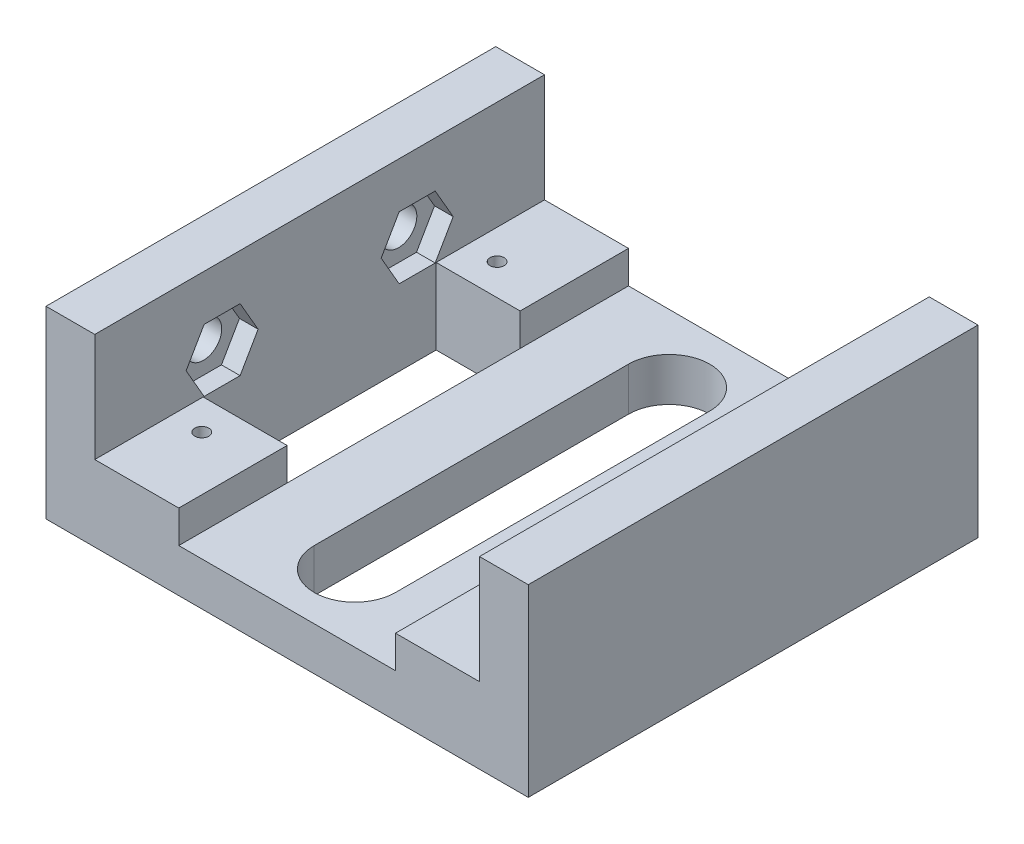
SolidWorks part; units mm, degrees
ref_plane "Front Plane" through (0, 0, 0) normal (0, 0, 1) x (1, 0, 0)
ref_plane "Top Plane" through (0, 0, 0) normal (0, 1, 0) x (1, 0, 0)
ref_plane "Right Plane" through (0, 0, 0) normal (1, 0, 0) x (0, 0, -1)
sketch "Sketch1" plane through (0, 0, 0) normal (0, 1, 0) x (1, 0, 0)
  line L9 (-44.5, 0) -> (44.5, 0)
  line L10 (-44.5, 0) -> (-44.5, 83)
  line L11 (-44.5, 83) -> (44.5, 83)
  line L12 (44.5, 0) -> (44.5, 83)
  line L13 (34.5, 0) -> (-34.5, 0) construction
  line L14 (34.5, 0) -> (34.5, 83) construction
  line L15 (34.5, 83) -> (-34.5, 83) construction
  line L16 (-34.5, 0) -> (-34.5, 83) construction
  line L21 (-30, 14.25) -> (30, 14.25) construction
  line L22 (-30, 14.25) -> (-30, 68.75) construction
  line L23 (-30, 68.75) -> (30, 68.75) construction
  line L24 (30, 14.25) -> (30, 68.75) construction
  line L27 (-7.5, 70.5) -> (-7.5, 12.5)
  line L29 (7.5, 12.5) -> (7.5, 70.5)
  circle A0 centre (30, 14.25) radius 1.3
  circle A1 centre (-30, 14.25) radius 1.3
  circle A2 centre (-30, 68.75) radius 1.3
  circle A3 centre (30, 68.75) radius 1.3
  circle A4 centre (-30, 68.75) radius 1.75 construction
  circle A6 centre (0, 70.5) radius 7.5
  circle A7 centre (0, 12.5) radius 7.5
  point P9 (0, 0)
  point P10 (0, 0)
  point P25 (0, 14.25)
  point P27 (44.5, 41.5)
  point P28 (30, 41.5)
  point P31 (0, 39.8535)
  point P32 (0, 58.9503)
  point P33 (7.7128, 21.3182)
  point P34 (8.3612, 44.0115)
  point P35 (15.4007, 27.5241)
  point P36 (0, 0)
  point P37 (-7.5, 51.2206)
  dimension "D7" = 2.6
  dimension "D8" = 3.5
  dimension "D1" = 83
  dimension "D2" = 69
  dimension "D3" = 10
  dimension "D4" = 15
  dimension "D5" = 5
  dimension "D6" = 5
  dimension "D9" = 60
  dimension "D10" = 54.5
extrude "Main Body" add sketch "Sketch1" along normal blind 14
sketch "Sketch2" plane through (0, 14, 0) normal (0, 1, 0) x (1, 0, 0)
  line L1 (-20, 0) -> (20, 0)
  line L2 (-20, 0) -> (-20, 83)
  line L3 (-20, 83) -> (20, 83)
  line L4 (20, 0) -> (20, 83)
  line L7 (-44.5, 83) -> (44.5, 83) construction
  point P8 (0, 0)
  dimension "D1" = 40
extrude "Screw Groove" cut sketch "Sketch2" against normal blind 6
sketch "Sketch4" plane through (0, 14, 0) normal (0, 1, 0) x (1, 0, 0)
  line L0 (-44.5, 0) -> (-20, 0) construction
  line L1 (-44.5, 83) -> (-35.5, 83)
  line L2 (-44.5, 83) -> (-44.5, 0)
  line L3 (-44.5, 0) -> (-35.5, 0)
  line L4 (-35.5, 83) -> (-35.5, 0)
  line L5 (20, 83) -> (44.5, 83) construction
  line L6 (44.5, 0) -> (35.5, 0)
  line L7 (44.5, 0) -> (44.5, 83)
  line L8 (44.5, 83) -> (35.5, 83)
  line L9 (35.5, 0) -> (35.5, 83)
  dimension "D1" = 71
extrude "Mount Lift" add sketch "Sketch4" along normal offset from surface (20 mm away) 34 up to face at (0, 0, -41.5)
ref_plane "Plane1" through (-38.9438, 0, 0) normal (-1, 0, 0) x (0, 0, 1)
sketch "Sketch6" plane through (-44.5, 0, 0) normal (-1, 0, 0) x (0, 0, 1)
  line L0 (-52.8551, 19.7547) -> (-56.1775, 25.5094)
  line L1 (-53.0842, 19.7547) -> (-56.2921, 25.3109) construction
  line L2 (-56.2921, 25.3109) -> (-62.7079, 25.3109) construction
  line L3 (-62.7079, 25.3109) -> (-65.9158, 19.7547) construction
  line L4 (-65.9158, 19.7547) -> (-62.7079, 14.1984) construction
  line L5 (-62.7079, 14.1984) -> (-56.2921, 14.1984) construction
  line L6 (-56.2921, 14.1984) -> (-53.0842, 19.7547) construction
  line L7 (-56.1775, 25.5094) -> (-62.8225, 25.5094)
  line L8 (-62.8225, 25.5094) -> (-66.1449, 19.7547)
  line L9 (-66.1449, 19.7547) -> (-62.8225, 14)
  line L10 (-62.8225, 14) -> (-56.1775, 14)
  line L11 (-56.1775, 14) -> (-52.8551, 19.7547)
  line L12 (-23.5, 19.7547) -> (-59.5, 19.7547) construction
  line L13 (-16.8551, 19.7547) -> (-20.1775, 25.5094)
  line L14 (-20.1775, 25.5094) -> (-26.8225, 25.5094)
  line L15 (-26.8225, 25.5094) -> (-30.1449, 19.7547)
  line L16 (-30.1449, 19.7547) -> (-26.8225, 14)
  line L17 (-26.8225, 14) -> (-20.1775, 14)
  line L18 (-20.1775, 14) -> (-16.8551, 19.7547)
  line L19 (0, 0) -> (-83, 0) construction
  line L23 (-12.95, 14) -> (-15.55, 14) construction
  circle A0 centre (-59.5, 19.7547) radius 5.5563 construction
  circle A1 centre (-23.5, 19.7547) radius 5.7547 construction
  point P26 (-41.5, 0)
  point P27 (-41.5, 19.7547)
  dimension "D1" = 11.1125
  dimension "D3" = 36
  dimension "D2" = 0.1984
extrude "Mount Nuts" cut sketch "Sketch6" against normal up to surface (18.9438 mm away) from surface at -5.5563 up to face at (-20, 11, -41.5) starting at plane "Plane1"
sketch "Sketch5" plane through (-38.9438, 0, 0) normal (-1, 0, 0) x (0, 0, 1)
  line L0 (0, 0) -> (-83, 0) construction
  line L1 (-20.1775, 14) -> (-26.8225, 25.5094) construction
  line L4 (-59.5, 19.7547) -> (-23.5, 19.7547) construction
  circle A0 centre (-59.5, 19.7547) radius 3.175 construction
  circle A1 centre (-23.5, 19.7547) radius 3.175 construction
  circle A2 centre (-59.5, 19.7547) radius 3.3734
  circle A3 centre (-23.5, 19.7547) radius 3.3734
  circle A4 centre (-23.5, 19.7547) radius 7.9375 construction
  circle A5 centre (-59.5, 19.7547) radius 7.9375 construction
  point P2 (-23.5, 19.7547)
  point P3 (-41.5, 0)
  point P4 (-41.5, 19.7547)
  dimension "D2" = 6.35
  dimension "D5" = 15.875
  dimension "D3" = 0.1984
extrude "9/32 Mount Holes" cut sketch "Sketch5" along normal up to next
sketch "Sketch8" plane through (0, 14, 0) normal (0, 1, 0) x (1, 0, 0)
  line L33 (-20, 0) -> (20, 0) construction
  line L34 (-35.5, 20) -> (35.5, 20) construction
  line L35 (-35.5, 20) -> (-35.5, 63) construction
  line L36 (-35.5, 63) -> (35.5, 63) construction
  line L37 (35.5, 20) -> (35.5, 63) construction
  line L38 (20, 83) -> (-20, 83) construction
  line L39 (35.5, 83) -> (35.5, 0) construction
  line L40 (-35.5, 0) -> (-35.5, 83) construction
  line L41 (-20, 83) -> (-20, 0) construction
  line L42 (-35.5, 63) -> (-20, 63)
  line L43 (-35.5, 63) -> (-35.5, 20)
  line L44 (-35.5, 20) -> (-20, 20)
  line L45 (-20, 63) -> (-20, 20)
  line L46 (20, 0) -> (20, 83) construction
  line L47 (35.5, 63) -> (20, 63)
  line L48 (35.5, 63) -> (35.5, 20)
  line L49 (35.5, 20) -> (20, 20)
  line L50 (20, 63) -> (20, 20)
  dimension "D1" = 20
  dimension "D2" = 20
extrude "Middle Cut" cut sketch "Sketch8" against normal up to surface (14 mm away) up to face at (0, 0, -41.5)
